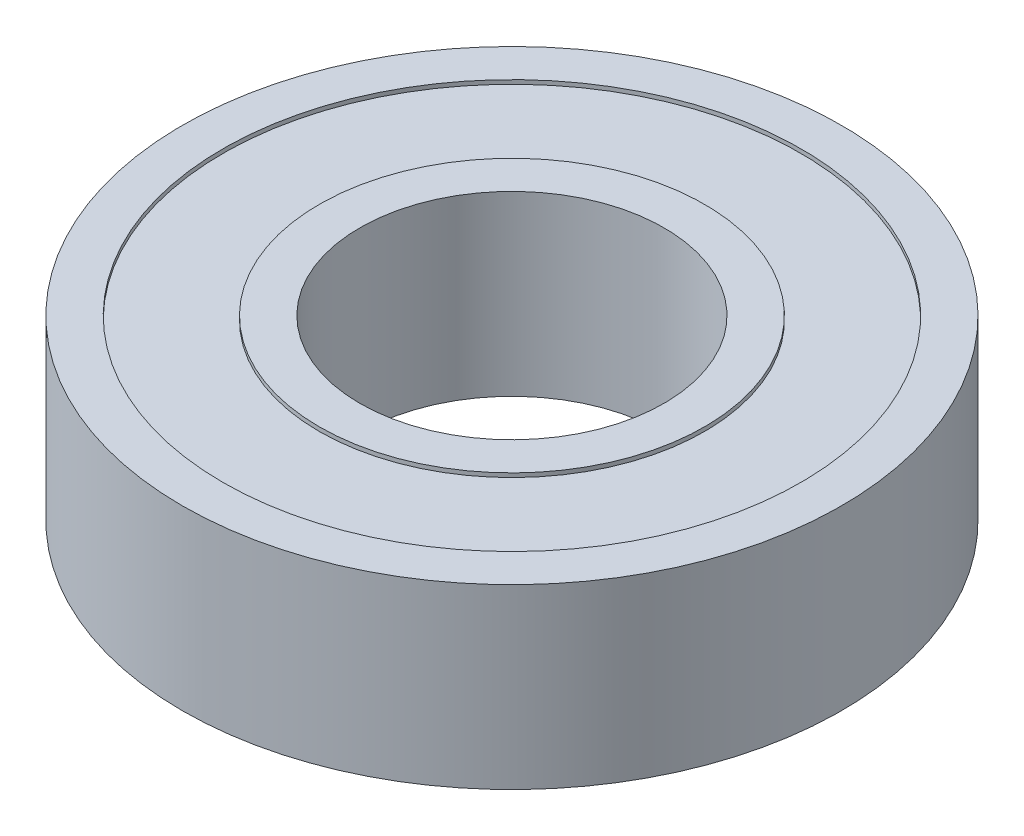
SolidWorks part; units mm, degrees
ref_plane "Front Plane" through (0, 0, 0) normal (0, 0, 1) x (1, 0, 0)
ref_plane "Top Plane" through (0, 0, 0) normal (0, 1, 0) x (1, 0, 0)
ref_plane "Right Plane" through (0, 0, 0) normal (1, 0, 0) x (0, 0, -1)
sketch "Sketch1" plane through (0, 0, 0) normal (0, 0, 1) x (1, 0, 0)
  line L0 (0, 28.6206) -> (0, -27.6052) construction
  line L1 (0, -55) -> (0, 55) construction
  line L2 (9.525, 0) -> (20.6375, 0)
  line L3 (20.6375, 0) -> (20.6375, 5.5562)
  line L4 (20.6375, 5.5562) -> (18.0975, 5.5562)
  line L5 (18.0975, 5.5562) -> (18.0975, 5.3022)
  line L6 (18.0975, 5.3022) -> (12.065, 5.3022)
  line L7 (12.065, 5.3022) -> (12.065, 5.5562)
  line L8 (12.065, 5.5562) -> (9.525, 5.5562)
  line L9 (55, 0) -> (-55, 0) construction
  line L10 (-16.0643, 0) -> (47.5798, 0) construction
  line L11 (9.525, 0) -> (9.525, 5.5562)
  dimension "D1" = 41.275
  dimension "D2" = 24.13
  dimension "D3" = 36.195
  dimension "D4" = 19.05
  dimension "D5" = 11.1125
  dimension "D6" = 0.254
revolve "Revolve1" add sketch "Sketch1" angle 360 about L0
mirror "Mirror1" about plane through (0, 0, 0) normal (0, 1, 0) of "Revolve1"
